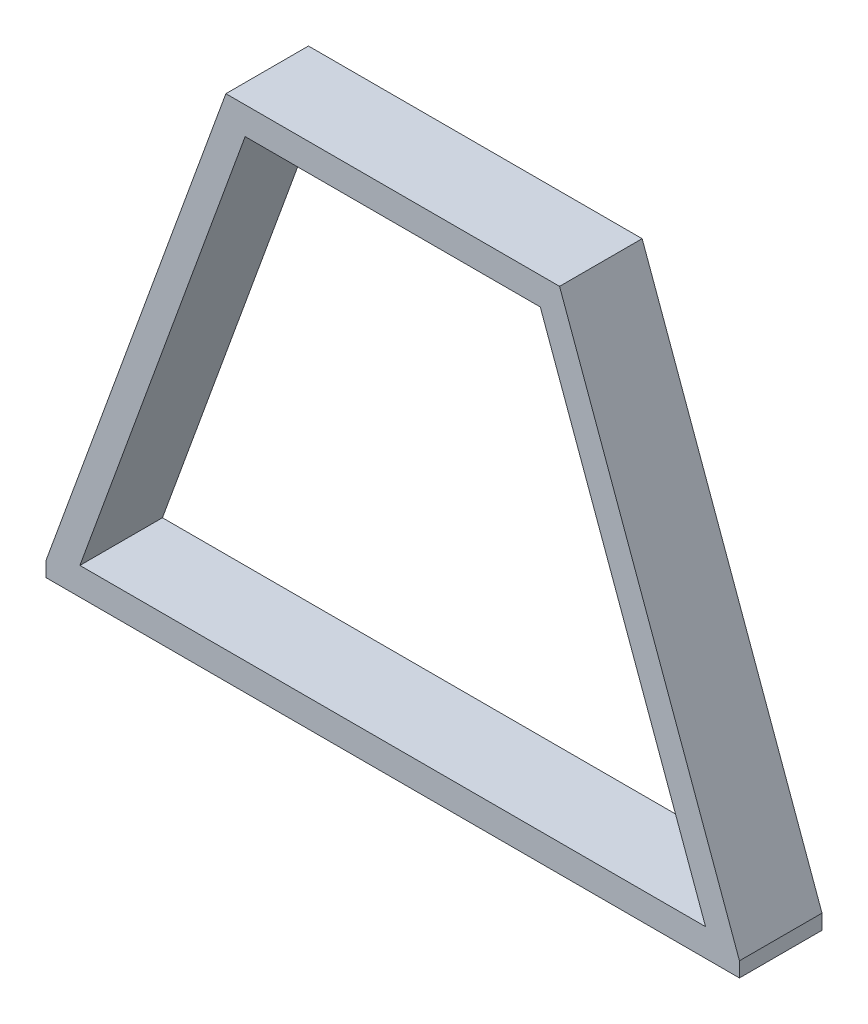
SolidWorks part; units mm, degrees
ref_plane "Alzado" through (0, 0, 0) normal (0, 0, 1) x (1, 0, 0)
ref_plane "Planta" through (0, 0, 0) normal (0, 1, 0) x (1, 0, 0)
ref_plane "Vista lateral" through (0, 0, 0) normal (1, 0, 0) x (0, 0, -1)
sketch "Croquis1" plane through (0, 0, 0) normal (0, 0, 1) x (1, 0, 0)
  line L0 (0, 0) -> (650, 0)
  line L1 (0, 0) -> (171.0101, 469.8463)
  line L2 (650, 0) -> (478.9899, 469.8463)
  line L3 (171.0101, 469.8463) -> (478.9899, 469.8463)
  line L4 (188.7953, 444.4463) -> (461.2047, 444.4463)
  line L5 (613.725, 25.4) -> (461.2047, 444.4463)
  line L6 (36.275, 25.4) -> (613.725, 25.4)
  line L7 (36.275, 25.4) -> (188.7953, 444.4463)
  dimension "D1" = 650
  dimension "D2" = 70
  dimension "D3" = 500
  dimension "D4" = 70
  dimension "D5" = 25.4
extrude "Saliente-Extruir1" add sketch "Croquis1" along normal blind 76.2
sketch "Croquis2" plane through (0, 0, 0) normal (0, -1, 0) x (1, 0, 0)
  line L0 (0, 0) -> (650, 0) construction
  line L1 (0, 76.2) -> (5, 76.2)
  line L2 (0, 76.2) -> (0, 0)
  line L3 (0, 0) -> (5, 0)
  line L4 (5, 76.2) -> (5, 0)
  line L6 (650, 76.2) -> (645, 76.2)
  line L7 (650, 76.2) -> (650, 0)
  line L8 (650, 0) -> (645, 0)
  line L9 (645, 76.2) -> (645, 0)
  dimension "D1" = 5
  dimension "D2" = 5
extrude "Cortar-Extruir1" cut sketch "Croquis2" against normal blind 76.2
